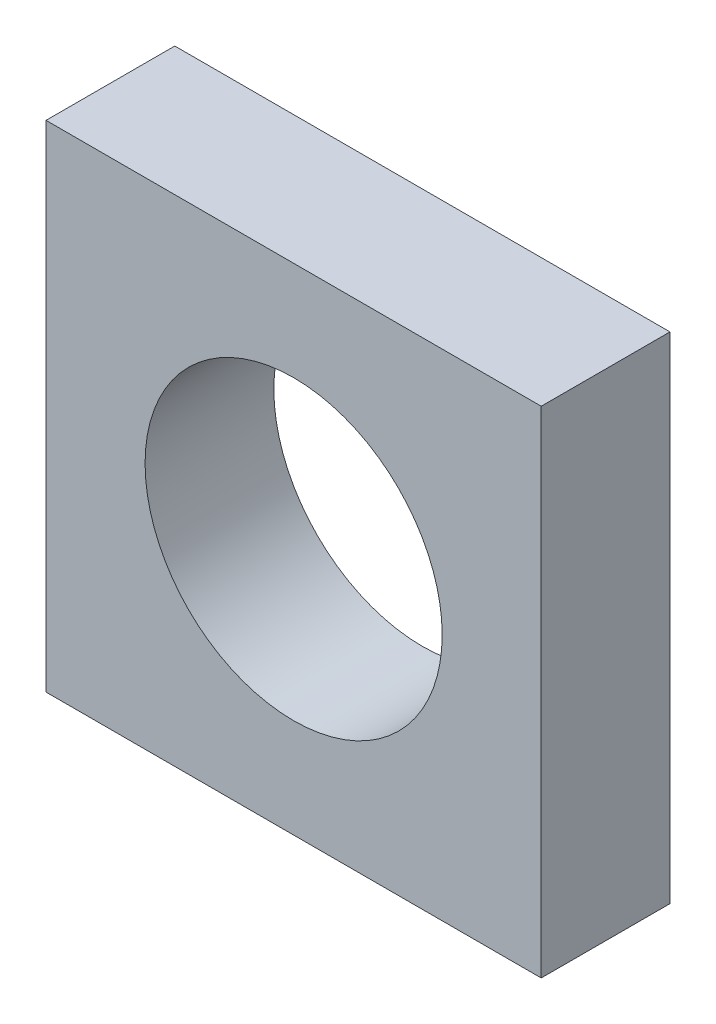
SolidWorks part; units mm, degrees
ref_plane "Front Plane" through (0, 0, 0) normal (0, 0, 1) x (1, 0, 0)
ref_plane "Top Plane" through (0, 0, 0) normal (0, 1, 0) x (1, 0, 0)
ref_plane "Right Plane" through (0, 0, 0) normal (1, 0, 0) x (0, 0, -1)
sketch "Sketch1" plane through (0, 0, 0) normal (0, 0, 1) x (1, 0, 0)
  line L1 (-25, 25) -> (25, 25)
  line L2 (-25, 25) -> (-25, -25)
  line L3 (-25, -25) -> (25, -25)
  line L4 (25, 25) -> (25, -25)
  line L5 (-25, 25) -> (25, -25) construction
  line L6 (-25, -25) -> (25, 25) construction
  circle A0 centre (0, 0) radius 15
  point P0 (0, 0)
  dimension "D3" = 30
  dimension "D1" = 50
  dimension "D2" = 50
extrude "Boss-Extrude1" add sketch "Sketch1" along normal blind 13
